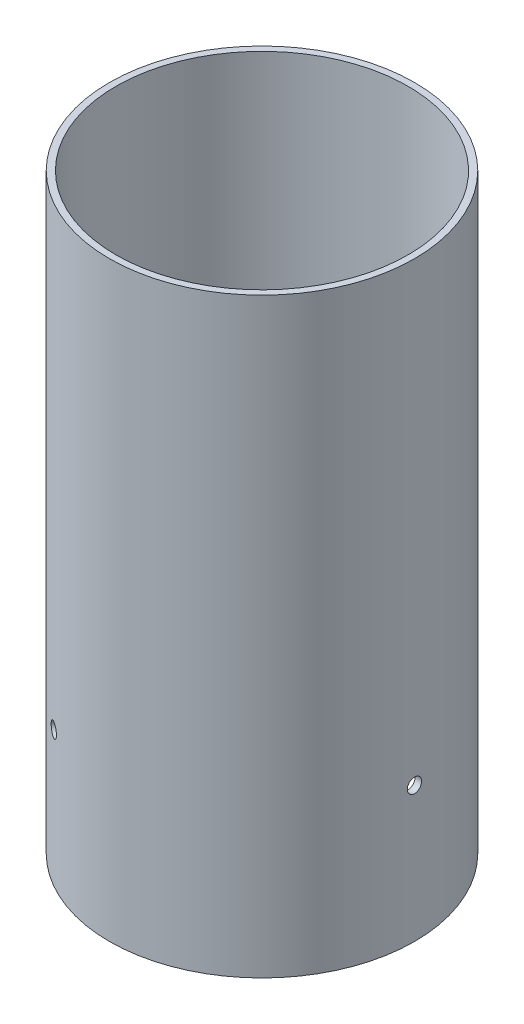
SolidWorks part; units mm, degrees
material "G10 Fiberglass"
ref_plane "Front Plane" through (0, 0, 0) normal (0, 0, 1) x (1, 0, 0)
ref_plane "Top Plane" through (0, 0, 0) normal (0, 1, 0) x (1, 0, 0)
ref_plane "Right Plane" through (0, 0, 0) normal (1, 0, 0) x (0, 0, -1)
sketch "Sketch1" plane through (0, 0, 0) normal (0, 1, 0) x (1, 0, 0)
  circle A0 centre (0, 0) radius 36.5125
  circle A1 centre (0, 0) radius 38.1381
  dimension "D1" = 73.025
  dimension "D2" = 1.6256
extrude "Boss-Extrude1" add sketch "Sketch1" along normal blind 147.8153
ref_axis "Axis1" through (0, 155.0861, 0) along (0, -1, 0)
ref_plane "Plane1" through (38.1381, 0, 0) normal (1, 0, 0) x (0, 0, -1)
sketch "Sketch2" plane through (38.1381, 0, 0) normal (1, 0, 0) x (0, 0, -1)
  line L0 (0, 155.0861) -> (0, -7.3851) construction
  circle A0 centre (0, 33.8074) radius 1.7859
  point P4 (0, 0)
  point P5 (0, 0)
  dimension "D1" = 3.5719
  dimension "D2" = 33.8074
extrude "Cut-Extrude1" cut sketch "Sketch2" against normal up to next
pattern_circular "CirPattern1" count 3 over 360 about axis through (0, 155.0861, 0) along (0, -1, 0) of "Cut-Extrude1"
